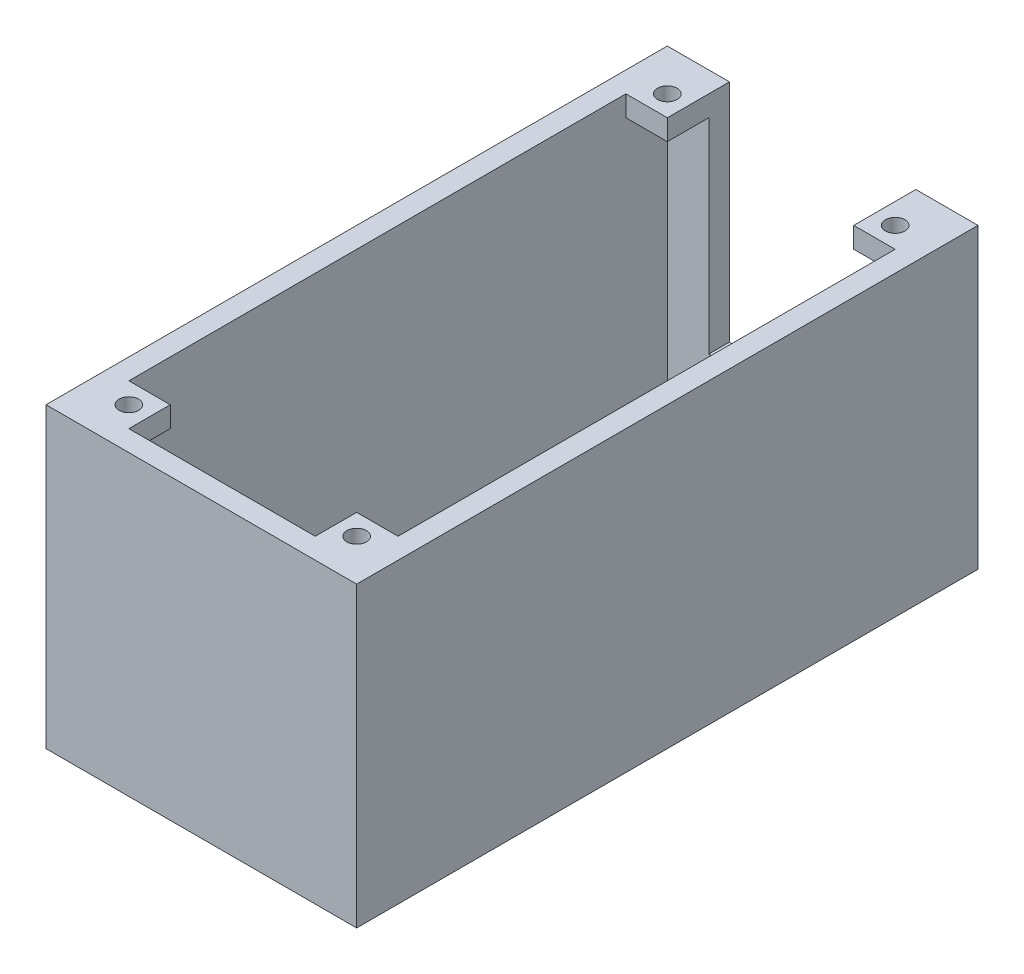
SolidWorks part; units mm, degrees
ref_plane "Front Plane" through (0, 0, 0) normal (0, 0, 1) x (1, 0, 0)
ref_plane "Top Plane" through (0, 0, 0) normal (0, 1, 0) x (1, 0, 0)
ref_plane "Right Plane" through (0, 0, 0) normal (1, 0, 0) x (0, 0, -1)
sketch "Sketch1" plane through (0, 0, 0) normal (0, 1, 0) x (1, 0, 0)
  line L1 (-19.05, -38.1) -> (19.05, -38.1)
  line L2 (-19.05, -38.1) -> (-19.05, 38.1)
  line L3 (-19.05, 38.1) -> (19.05, 38.1)
  line L4 (19.05, -38.1) -> (19.05, 38.1)
  line L5 (-19.05, -38.1) -> (19.05, 38.1) construction
  line L6 (-19.05, 38.1) -> (19.05, -38.1) construction
  point P0 (0, 0)
  dimension "D1" = 38.1
  dimension "D2" = 76.2
extrude "Boss-Extrude1" add sketch "Sketch1" along normal blind 2.54
hole_wizard "M2 Clearance Hole1 - to drone" positions "Sketch3" profile "Sketch4" hole size "M2" standard "ANSI Metric" end condition through all
sketch "Sketch3" plane through (0, 2.54, 0) normal (0, 1, 0) x (1, 0, 0)
  line L0 (-13.97, 0) -> (13.97, 0) construction
  point P0 (-13.97, 0)
  point P2 (13.97, 0)
  point P10 (0, 0)
  dimension "D1" = 27.94
sketch "Sketch4" plane through (-13.97, 2.54, 0) normal (1, 0, 0) x (0, 0, 1)
  line L0 (0, 0) -> (0, 2.54)
  line L1 (0, 2.54) -> (1.2, 2.54)
  line L2 (1.2, 2.54) -> (1.2, 0)
  line L5 (1.2, 0) -> (0, 0)
  line L11 (0, -6.35) -> (0, 107.95) construction
  dimension "Thru Hole Dia." = 2.4
  dimension "Thru Hole Depth" = 2.54
hole_wizard "M2 Clearance Hole2 - to Pi" positions "Sketch5" profile "Sketch6" hole size "M2" standard "ANSI Metric" end condition through all
sketch "Sketch5" plane through (0, 2.54, 0) normal (0, 1, 0) x (1, 0, 0)
  line L1 (-5.6998, -23.5001) -> (5.6998, -23.5001) construction
  line L2 (-5.6998, -23.5001) -> (-5.6998, 23.5001) construction
  line L3 (-5.6998, 23.5001) -> (5.6998, 23.5001) construction
  line L4 (5.6998, -23.5001) -> (5.6998, 23.5001) construction
  line L5 (-5.6998, -23.5001) -> (5.6998, 23.5001) construction
  line L6 (-5.6998, 23.5001) -> (5.6998, -23.5001) construction
  point P0 (-5.6998, 23.5001)
  point P2 (5.6998, 23.5001)
  point P4 (5.6998, -23.5001)
  point P6 (-5.6998, -23.5001)
  point P62 (0, 0)
  dimension "D1" = 11.3995
  dimension "D2" = 47.0002
sketch "Sketch6" plane through (-5.6998, 2.54, -23.5001) normal (1, 0, 0) x (0, 0, 1)
  line L0 (0, 0) -> (0, 2.54)
  line L1 (0, 2.54) -> (1.2, 2.54)
  line L2 (1.2, 2.54) -> (1.2, 0)
  line L5 (1.2, 0) -> (0, 0)
  line L11 (0, -6.35) -> (0, 107.95) construction
  dimension "Thru Hole Dia." = 2.4
  dimension "Thru Hole Depth" = 2.54
sketch "Sketch7" plane through (0, 2.54, 0) normal (0, 1, 0) x (1, 0, 0)
  line L0 (-19.05, -38.1) -> (-19.05, -35.56)
  line L1 (-19.05, 38.1) -> (-19.05, -38.1) construction
  line L2 (-16.51, -35.56) -> (16.51, -35.56)
  line L3 (19.05, -38.1) -> (19.05, 38.1) construction
  line L5 (19.05, -38.1) -> (-19.05, -38.1)
  line L6 (-16.51, -35.56) -> (-16.51, 38.1)
  line L7 (19.05, 38.1) -> (-19.05, 38.1) construction
  line L8 (-16.51, 38.1) -> (-19.05, 38.1)
  line L9 (-19.05, 38.1) -> (-19.05, -35.56)
  line L10 (19.05, -38.1) -> (19.05, 38.1)
  line L11 (19.05, 38.1) -> (16.51, 38.1)
  line L12 (16.51, 38.1) -> (16.51, -35.56)
  dimension "D1" = 2.54
extrude "Boss-Extrude2" add sketch "Sketch7" along normal blind 33.9852
sketch "Sketch9" plane through (0, 0, -38.1) normal (0, 0, -1) x (-1, 0, 0)
  line L2 (-11.43, 8.89) -> (11.43, 8.89)
  line L3 (16.51, 36.5252) -> (16.51, 2.54) construction
  line L5 (16.51, 2.54) -> (-16.51, 2.54)
  line L6 (-10.3149, 8.89) -> (-10.3149, 2.54) construction
  line L7 (10.3149, 8.89) -> (10.3149, 2.54) construction
  line L8 (-10.3149, 5.715) -> (10.3149, 5.715) construction
  line L9 (11.43, 8.89) -> (11.43, 36.5252)
  line L10 (-16.51, 36.5252) -> (16.51, 36.5252) construction
  line L11 (11.43, 36.5252) -> (16.51, 36.5252)
  line L12 (16.51, 36.5252) -> (16.51, 2.54)
  line L13 (-16.51, 36.5252) -> (-11.43, 36.5252)
  line L14 (-11.43, 36.5252) -> (-11.43, 8.89)
  line L15 (-16.51, 36.5252) -> (-16.51, 2.54)
  circle A0 centre (-10.3149, 5.715) radius 1.5011
  circle A1 centre (10.3149, 5.715) radius 1.5011
  point P19 (0, 5.715)
  dimension "D1" = 3.0023
  dimension "D3" = 20.6299
  dimension "D2" = 6.35
  dimension "D4" = 5.08
extrude "Boss-Extrude4" add sketch "Sketch9" against normal blind 2.54 separate body
ref_plane "Plane1" through (0, 19.5326, 0) normal (0, 1, 0) x (1, 0, 0)
sketch "Sketch11" plane through (0, 19.5326, 0) normal (0, 1, 0) x (1, 0, 0)
  line L0 (-16.51, -35.56) -> (-16.51, -29.464)
  line L1 (-16.51, -35.56) -> (-16.51, 38.1) construction
  line L2 (-16.51, -29.464) -> (16.51, -29.464)
  line L3 (16.51, -29.464) -> (16.51, -35.56)
  line L4 (16.51, -35.56) -> (-16.51, -35.56) construction
  line L5 (16.51, -35.56) -> (-16.51, -35.56)
  line L6 (-6.985, -31.75) -> (6.985, -31.75) construction
  line L7 (0, -29.464) -> (0, -35.56) construction
  line L8 (16.51, 38.1) -> (16.51, -35.56) construction
  line L9 (-6.985, -30.734) -> (6.985, -30.734) construction
  circle A0 centre (-6.985, -31.75) radius 1.016
  circle A1 centre (6.985, -31.75) radius 1.016
  point P18 (0, -31.75)
  dimension "D1" = 2.032
  dimension "D2" = 3.81
  dimension "D3" = 13.97
  dimension "D4" = 1.27
extrude "Boss-Extrude6" add sketch "Sketch11" against normal blind 2.54
sketch "Sketch12" plane through (0, 36.5252, 0) normal (0, 1, 0) x (1, 0, 0)
  line L1 (16.51, 38.1) -> (16.51, -35.56) construction
  line L4 (-16.51, 33.02) -> (16.51, 33.02) construction
  line L7 (-16.51, -35.56) -> (-16.51, 38.1) construction
  line L10 (-16.51, -30.48) -> (-11.43, -30.48)
  line L12 (16.51, -35.56) -> (16.51, -30.48)
  line L15 (11.43, -30.48) -> (11.43, -35.56)
  line L16 (16.51, -35.56) -> (-16.51, -35.56) construction
  line L17 (11.43, -35.56) -> (16.51, -35.56)
  line L18 (-16.51, -35.56) -> (-11.43, -35.56)
  line L19 (-11.43, -35.56) -> (-11.43, -30.48)
  line L21 (-16.51, -30.48) -> (-16.51, -35.56)
  line L22 (16.51, -30.48) -> (11.43, -30.48)
  line L23 (16.51, 35.56) -> (11.43, 35.56)
  line L24 (11.43, 35.56) -> (11.43, 30.48)
  line L25 (11.43, 30.48) -> (16.51, 30.48)
  line L26 (16.51, 30.48) -> (16.51, 35.56)
  line L27 (-16.51, 35.56) -> (-11.43, 35.56)
  line L28 (-16.51, 35.56) -> (-11.43, 35.56) construction
  line L29 (-11.43, 35.56) -> (-11.43, 38.1) construction
  line L30 (-11.43, 35.56) -> (-11.43, 30.48)
  line L31 (-11.43, 30.48) -> (-16.51, 30.48)
  line L32 (-16.51, 30.48) -> (-16.51, 35.56)
  line L65 (13.97, 38.1) -> (13.97, -33.02)
  line L66 (-13.97, -33.02) -> (-13.97, 38.1)
  line L67 (13.97, -33.02) -> (-13.97, -33.02)
  line L68 (13.97, 38.1) -> (13.97, -33.02) construction
  line L69 (-13.97, -33.02) -> (-13.97, 38.1) construction
  line L70 (13.97, -33.02) -> (-13.97, -33.02) construction
  dimension "D2" = 2.54
  dimension "D3" = 2.54
  dimension "D1" = 2.54
extrude "Boss-Extrude7" add sketch "Sketch12" against normal blind 2.54
hole_wizard "M2 Clearance Hole1" positions "Sketch13" profile "Sketch14" hole size "M2" standard "ANSI Metric"
sketch "Sketch13" plane through (0, 36.5252, 0) normal (0, 1, 0) x (1, 0, 0)
  line L0 (-16.51, 33.02) -> (16.51, 33.02) construction
  line L1 (13.97, -33.02) -> (-13.97, -33.02) construction
  line L2 (-13.97, -33.02) -> (-13.97, 38.1) construction
  line L3 (13.97, 38.1) -> (13.97, -33.02) construction
  point P0 (-13.97, 33.02)
  point P4 (13.97, 33.02)
  point P6 (13.97, -33.02)
  point P10 (-13.97, -33.02)
sketch "Sketch14" plane through (-13.97, 36.5252, -33.02) normal (1, 0, 0) x (0, 0, 1)
  line L0 (0, 0) -> (0, 3.261)
  line L1 (0, 3.261) -> (1.2, 2.54)
  line L2 (1.2, 2.54) -> (1.2, 0)
  line L5 (1.2, 0) -> (0, 0)
  line L10 (0, 3.261) -> (-1.2, 2.54) construction
  line L11 (0, -6.35) -> (0, 107.95) construction
  dimension "Hole Dia." = 2.4
  dimension "Hole Depth" = 2.54
  dimension "Drill Angle" = 118
equation "\"D1@Sketch9\"=2*0.0591in"
equation "\"Wall_Thickness\"=0.1"
equation "\"D1@Boss-Extrude4\"=\"Wall_Thickness\""
